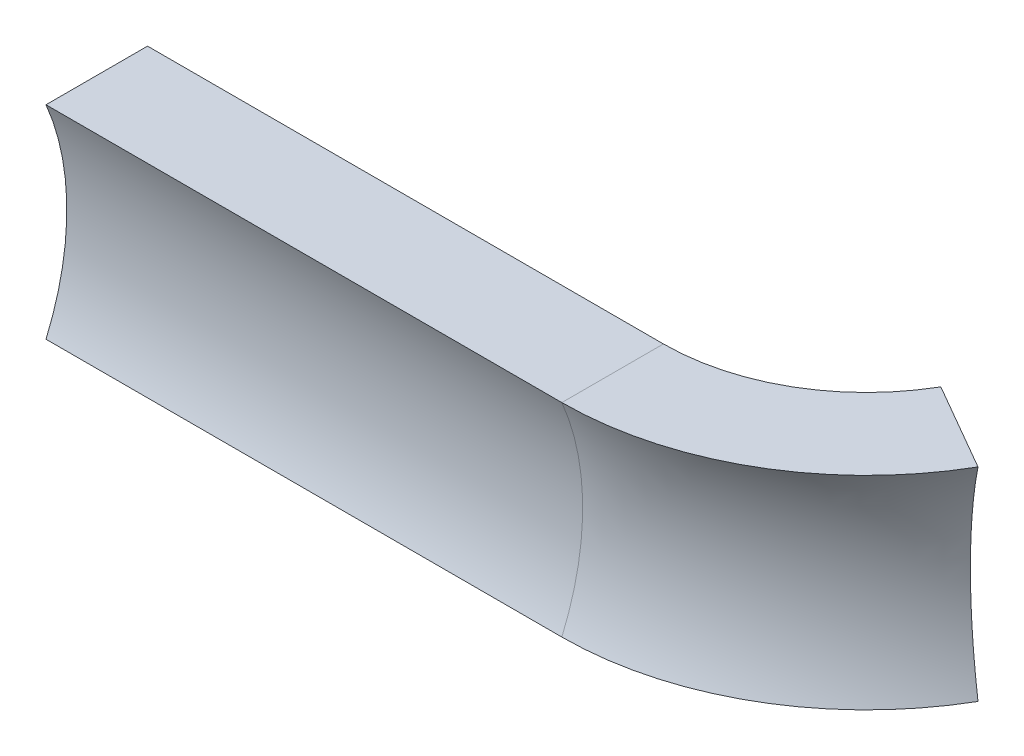
SolidWorks part; units mm, degrees
ref_plane "Front Plane" through (0, 0, 0) normal (0, 0, 1) x (1, 0, 0)
ref_plane "Top Plane" through (0, 0, 0) normal (0, 1, 0) x (1, 0, 0)
ref_plane "Right Plane" through (0, 0, 0) normal (1, 0, 0) x (0, 0, -1)
sketch "Sketch1" plane through (0, 0, 0) normal (0, 1, 0) x (1, 0, 0)
  line L0 (0, 0) -> (25.4, 0)
  line L1 (25.4, 10) -> (25.4, 0) construction
  line L2 (25.4, 10) -> (34.0603, 5) construction
  arc A0 (25.4, 0) -> (34.0603, 5) centre (25.4, 10) ccw
  point P3 (18.4342, 5)
  point P5 (23.0524, 5)
  point P7 (0, 0)
  point P8 (0, 0)
  point P9 (0, 0)
  point P10 (0, 0)
  dimension "D2" = 10
  dimension "D1" = 25.4
  dimension "D3" = 60
sketch "Sketch2" plane through (0, 0, 0) normal (1, 0, 0) x (0, 0, -1)
  line L0 (0, 5) -> (0, -5)
  line L1 (0, -5) -> (-5, -5)
  line L2 (0, 5) -> (-5, 5)
  arc A0 (-5, 5) -> (-5, -5) centre (-16.6743, 0) cw
  point P4 (0, 0)
  point P7 (0, 0)
  point P8 (0, 5.6745)
  dimension "D2" = 12.7
  dimension "D1" = 5
  dimension "D3" = 10
sweep "Sweep1" add profiles "Sketch2" path "Sketch1"
